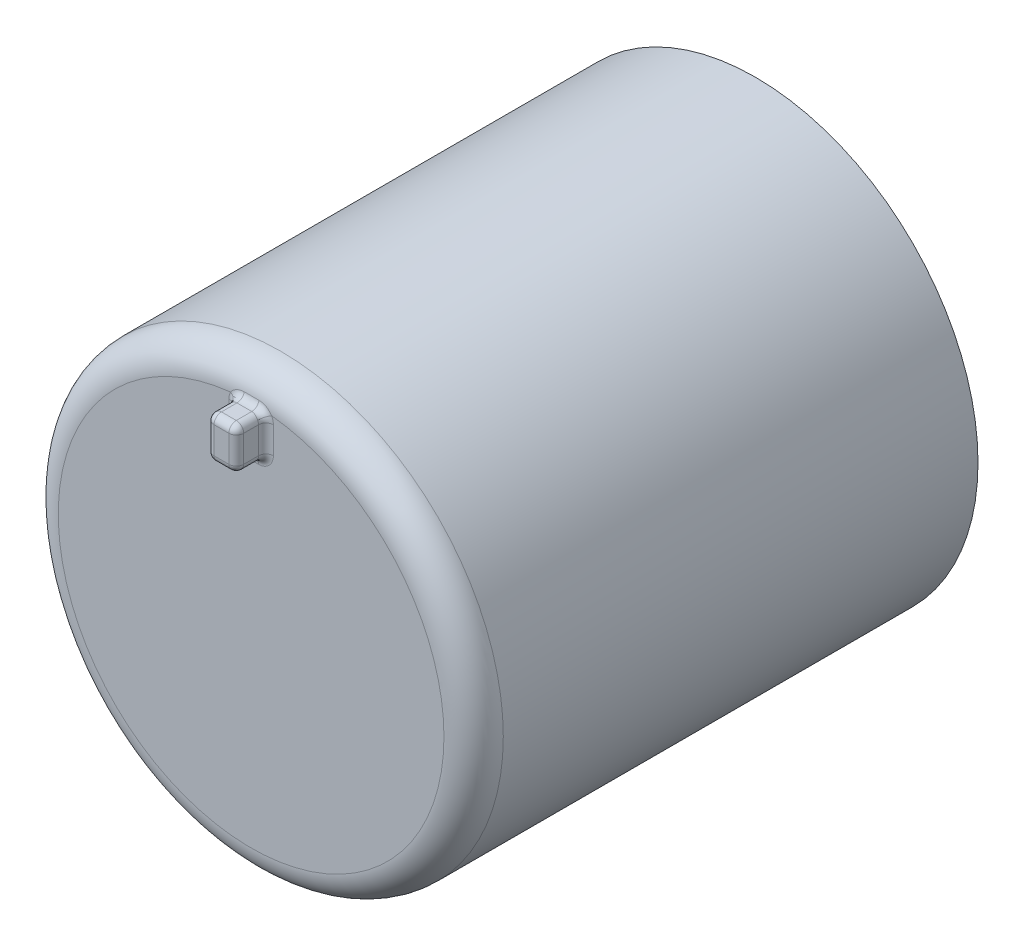
SolidWorks part; units mm, degrees
ref_plane "Plan de face" through (0, 0, 0) normal (0, 0, 1) x (1, 0, 0)
ref_plane "Plan de dessus" through (0, 0, 0) normal (0, 1, 0) x (1, 0, 0)
ref_plane "Plan de droite" through (0, 0, 0) normal (1, 0, 0) x (0, 0, -1)
sketch "Esquisse1" plane through (0, 0, 0) normal (0, 0, 1) x (1, 0, 0)
  circle A0 centre (0, 0) radius 7.5
  circle A1 centre (0, 0) radius 2.75
  dimension "D1" = 5.5
  dimension "D2" = 15
extrude "Boss.-Extru.1" add sketch "Esquisse1" along normal blind 15
sketch "Esquisse2" plane through (0, 0, 15) normal (0, 0, 1) x (1, 0, 0)
  circle A0 centre (0, 0) radius 7.5
extrude "Boss.-Extru.2" add sketch "Esquisse2" along normal blind 2
fillet "Congé1" radius 1 1 edges at (7.5, 0, 17)
sketch "Esquisse3" plane through (0, 0, 17) normal (0, 0, 1) x (1, 0, 0)
  line L1 (-0.5, 6.4807) -> (0.5, 6.4807)
  line L2 (-0.5, 6.4807) -> (-0.5, 5.0748)
  line L3 (-0.5, 5.0748) -> (0.5, 5.0748)
  line L4 (0.5, 6.4807) -> (0.5, 5.0748)
  circle A1 centre (0, 0) radius 6.5 construction
  dimension "D1" = 1
  dimension "D2" = 6.5
  dimension "D3" = 0.5
extrude "Boss.-Extru.3" add sketch "Esquisse3" along normal blind 1
fillet "Congé2" radius 0.25 8 edges at (0, 6.4807, 18) (-0.5, 6.4807, 17.5) (0.5, 6.4807, 17.5) (-0.5, 5.7778, 18) (-0.5, 5.0748, 17.5) (0, 5.0748, 18) (0.5, 5.0748, 17.5) (0.5, 5.7778, 18)
fillet "Congé3" radius 0.25 8 edges at (0.4268, 5.1481, 17) (0, 5.0748, 17) (-0.4268, 5.1481, 17) (-0.5, 5.7778, 17) (-0.4268, 6.4075, 17) (0, 6.4807, 17) (0.4268, 6.4075, 17) (0.5, 5.7778, 17)
